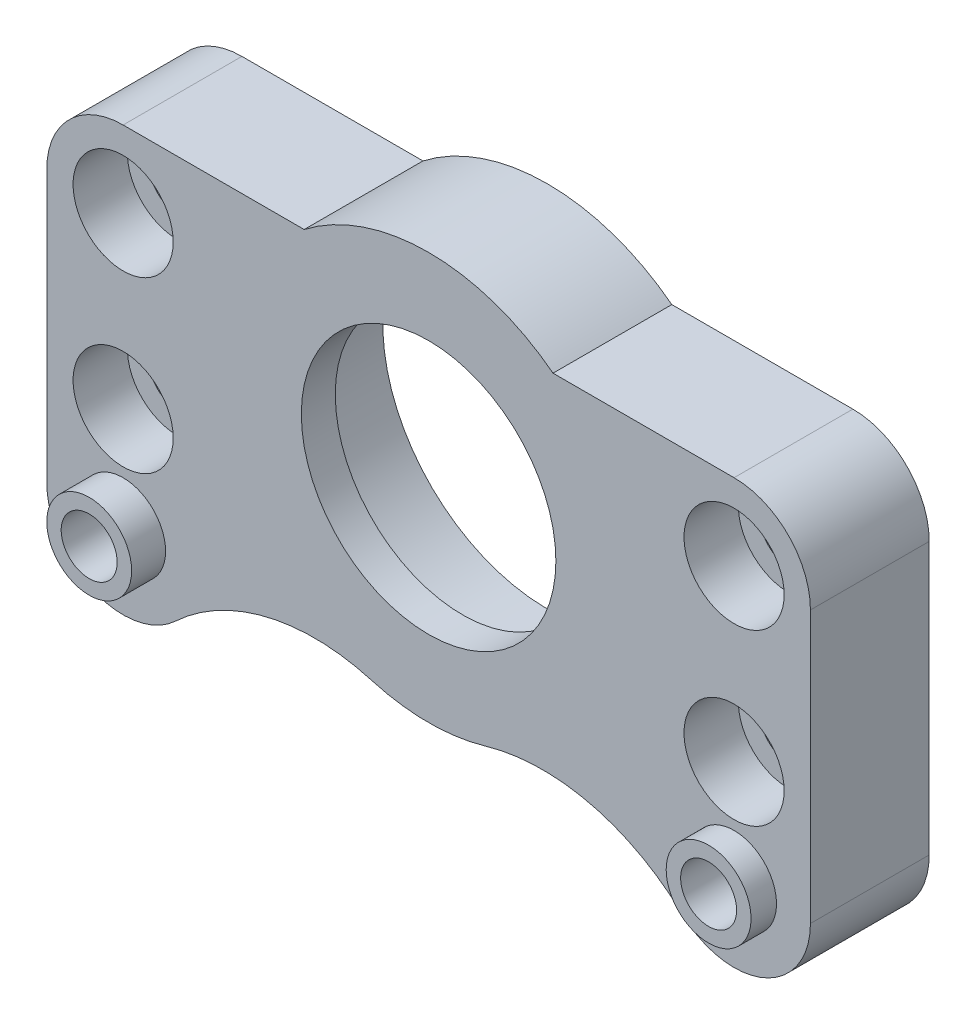
SolidWorks part; units mm, degrees
ref_plane "Front Plane" through (0, 0, 0) normal (0, 0, 1) x (1, 0, 0)
ref_plane "Top Plane" through (0, 0, 0) normal (0, 1, 0) x (1, 0, 0)
ref_plane "Right Plane" through (0, 0, 0) normal (1, 0, 0) x (0, 0, -1)
sketch "Sketch1" plane through (0, 0, 0) normal (0, 0, 1) x (1, 0, 0)
  circle A0 centre (0, 0) radius 9.5 construction
  circle A1 centre (0, 0) radius 2.5 construction
  dimension "D1" = 19
  dimension "D2" = 5
sketch "Sketch2" plane through (0, 0, 0) normal (0, 0, 1) x (1, 0, 0)
  line L0 (0, 0) -> (0, 12) construction
  line L1 (-7.3314, 9.5) -> (-18, 9.5)
  line L2 (-22.5, 0) -> (0, 0) construction
  line L3 (-22.5, 5) -> (-22.5, -11)
  line L5 (22.5, 5) -> (22.5, -11)
  line L6 (7.3314, 9.5) -> (18, 9.5)
  arc A0 (7.3314, 9.5) -> (-7.3314, 9.5) centre (0, 0) ccw
  circle A2 centre (0, 0) radius 9.5 construction
  arc A3 (-18, 9.5) -> (-22.5, 5) centre (-18, 5) ccw
  circle A4 centre (-18, 5) radius 1.65
  arc A5 (-22.5, -11) -> (-14.9232, -14.2838) centre (-18, -11) ccw
  circle A6 centre (-18, -11) radius 1.65
  circle A7 centre (-18, -5) radius 1.65
  arc A8 (-3.3592, -11.5202) -> (3.3592, -11.5202) centre (0, 0) ccw
  circle A12 centre (18, -5) radius 1.65
  circle A13 centre (18, -11) radius 1.65
  arc A14 (22.5, -11) -> (14.9232, -14.2838) centre (18, -11) cw
  circle A15 centre (18, 5) radius 1.65
  arc A16 (18, 9.5) -> (22.5, 5) centre (18, 5) cw
  arc A17 (-14.9232, -14.2838) -> (-3.3592, -11.5202) centre (-6.7183, -23.0405) cw
  arc A18 (14.9232, -14.2838) -> (3.3592, -11.5202) centre (6.7183, -23.0405) ccw
  dimension "D1" = 2.5
  dimension "D2" = 4.5
  dimension "D3" = 3.3
  dimension "D4" = 4.5
  dimension "D7" = 2.5
  dimension "D8" = 12
  dimension "D5" = 10
  dimension "D6" = 6
  dimension "D9" = 45
extrude "Boss-Extrude1" add sketch "Sketch2" along normal blind 7
sketch "Sketch3" plane through (0, 0, 0) normal (0, 0, 1) x (1, 0, 0)
  circle A2 centre (0, 0) radius 9.7
  circle A3 centre (0, 0) radius 9.7
  dimension "D1" = 0.2
extrude "Cut-Extrude1" cut sketch "Sketch3" along normal blind 5
sketch "Sketch4" plane through (0, 0, 5) normal (0, 0, -1) x (-1, 0, 0)
  circle A0 centre (0, 0) radius 7.5
  dimension "D1" = 15
extrude "Cut-Extrude2" cut sketch "Sketch4" against normal blind 5
sketch "Sketch6" plane through (0, 0, 0) normal (0, 0, -1) x (-1, 0, 0)
  line L0 (0, 0) -> (0, 12) construction
  line L1 (-16.3257, -8.1) -> (-19.6743, -8.1)
  line L2 (-19.6743, -8.1) -> (-21.3486, -11)
  line L3 (-21.3486, -11) -> (-19.6743, -13.9)
  line L4 (-19.6743, -13.9) -> (-16.3257, -13.9)
  line L5 (-16.3257, -13.9) -> (-14.6514, -11)
  line L6 (-14.6514, -11) -> (-16.3257, -8.1)
  line L7 (14.6514, -11) -> (16.3257, -8.1)
  line L8 (16.3257, -13.9) -> (14.6514, -11)
  line L9 (19.6743, -13.9) -> (16.3257, -13.9)
  line L10 (21.3486, -11) -> (19.6743, -13.9)
  line L11 (19.6743, -8.1) -> (21.3486, -11)
  line L12 (16.3257, -8.1) -> (19.6743, -8.1)
  circle A0 centre (-18, -11) radius 2.9 construction
  arc A1 (7.3314, 9.5) -> (-7.3314, 9.5) centre (0, 0) ccw construction
  circle A2 centre (18, -11) radius 2.9 construction
  dimension "D1" = 5.8
extrude "Cut-Extrude3" cut sketch "Sketch6" against normal blind 2.5
sketch "Sketch8" plane through (0, 0, 7) normal (0, 0, 1) x (1, 0, 0)
  circle A0 centre (18, -5) radius 2.95
  circle A1 centre (18, 5) radius 2.95
  circle A2 centre (-18, 5) radius 2.95
  circle A3 centre (-18, -5) radius 2.95
  dimension "D1" = 5.9
extrude "Cut-Extrude4" cut sketch "Sketch8" against normal blind 3.2
sketch "Sketch9" plane through (0, 0, 7) normal (0, 0, 1) x (1, 0, 0)
  line L0 (0, 0) -> (0, 7.5) construction
  circle A0 centre (-18, -11) radius 1.65
  circle A1 centre (-18, -11) radius 2.5
  circle A3 centre (-18, -11) radius 1.65 construction
  circle A4 centre (0, 0) radius 7.5 construction
  circle A5 centre (18, -11) radius 2.5
  circle A6 centre (18, -11) radius 1.65
  dimension "D1" = 5
extrude "Boss-Extrude2" add sketch "Sketch9" along normal blind 1.5
other "Move Face1" face at (-15.5, -11, 8.5) parameters "D1"=0.5
